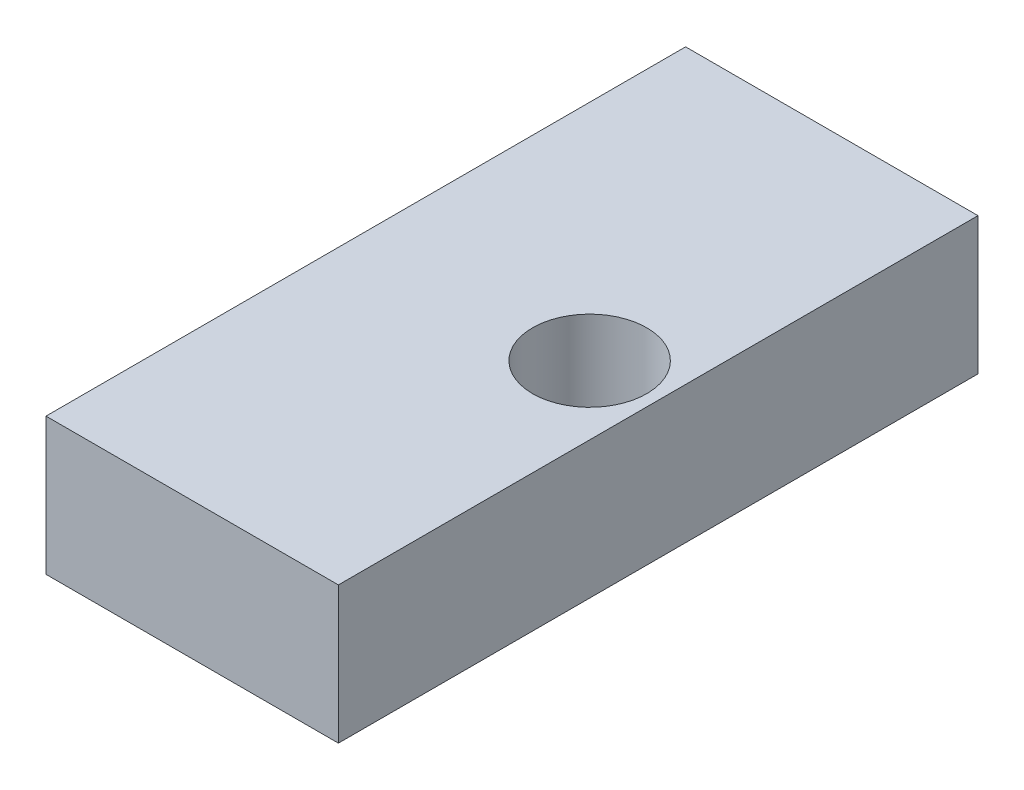
SolidWorks part; units mm, degrees
material "Pine"
ref_plane "Front Plane" through (0, 0, 0) normal (0, 0, 1) x (1, 0, 0)
ref_plane "Top Plane" through (0, 0, 0) normal (0, 1, 0) x (1, 0, 0)
ref_plane "Right Plane" through (0, 0, 0) normal (1, 0, 0) x (0, 0, -1)
sketch "Sketch1" plane through (0, 0, 0) normal (0, 0, 1) x (1, 0, 0)
  line L1 (-20.32, 9.525) -> (20.32, 9.525)
  line L2 (-20.32, 9.525) -> (-20.32, -9.525)
  line L3 (-20.32, -9.525) -> (20.32, -9.525)
  line L4 (20.32, 9.525) -> (20.32, -9.525)
  line L5 (-20.32, 9.525) -> (20.32, -9.525) construction
  line L6 (-20.32, -9.525) -> (20.32, 9.525) construction
  point P0 (0, 0)
  dimension "D1" = 40.64
  dimension "D2" = 19.05
extrude "Boss-Extrude1" add sketch "Sketch1" against normal blind 88.9
sketch "Sketch3" plane through (0, 9.525, 0) normal (0, 1, 0) x (1, 0, 0)
  circle A0 centre (10.795, 44.45) radius 7.9375
  dimension "D1" = 15.875
extrude "Cut-Extrude1" cut sketch "Sketch3" against normal through all
